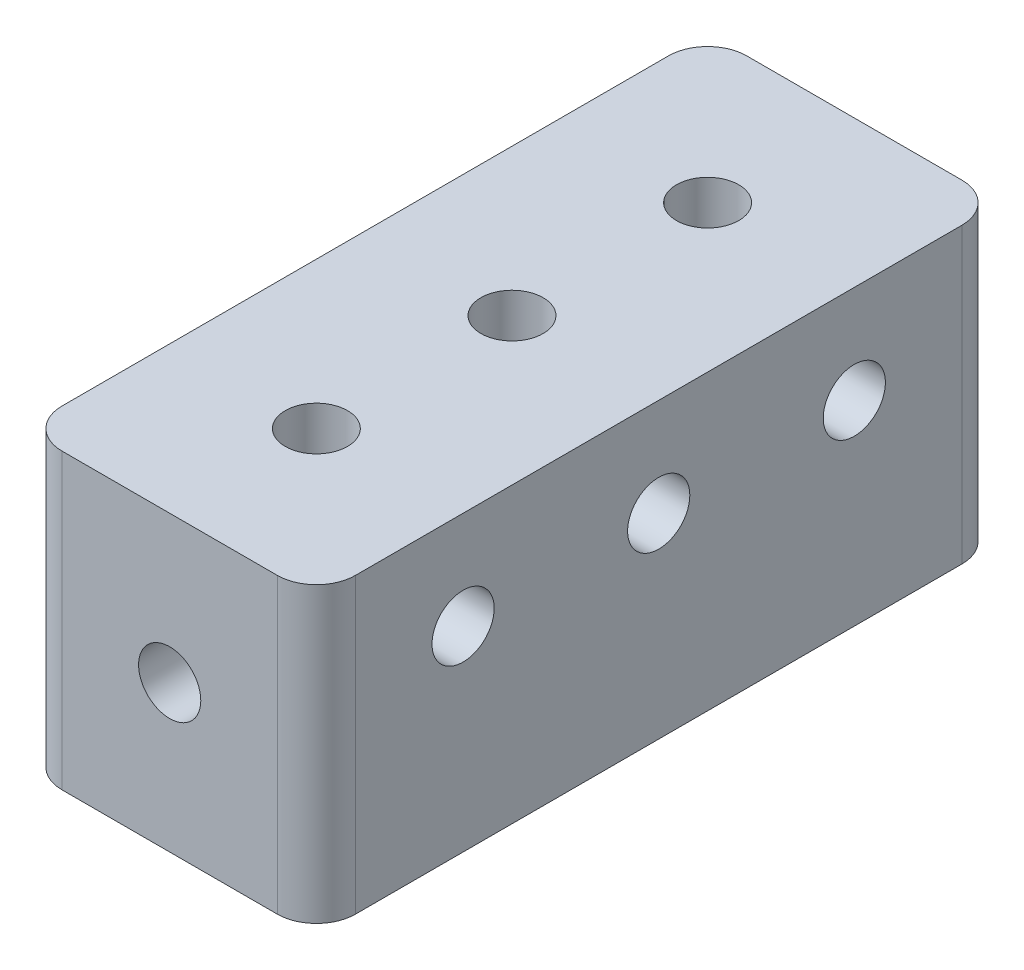
SolidWorks part; units mm, degrees
material "6061-T6 (SS)"
ref_plane "Front Plane" through (0, 0, 0) normal (0, 0, 1) x (1, 0, 0)
ref_plane "Top Plane" through (0, 0, 0) normal (0, 1, 0) x (1, 0, 0)
ref_plane "Right Plane" through (0, 0, 0) normal (1, 0, 0) x (0, 0, -1)
sketch "Sketch1" plane through (0, 0, 0) normal (0, 1, 0) x (1, 0, 0)
  line L1 (-9.525, -22.225) -> (9.525, -22.225)
  line L2 (-9.525, -22.225) -> (-9.525, 22.225)
  line L3 (-9.525, 22.225) -> (9.525, 22.225)
  line L4 (9.525, -22.225) -> (9.525, 22.225)
  line L5 (-9.525, -22.225) -> (9.525, 22.225) construction
  line L6 (-9.525, 22.225) -> (9.525, -22.225) construction
  point P0 (0, 0)
  dimension "D1" = 19.05
  dimension "D2" = 44.45
extrude "Boss-Extrude1" add sketch "Sketch1" along normal mid plane 19.05
sketch "Sketch2" plane through (0, 0, 22.225) normal (0, 0, 1) x (1, 0, 0)
  circle A0 centre (0, 0) radius 2.0193
  dimension "D3" = 4.0386
extrude "Cut-Extrude1" cut sketch "Sketch2" against normal blind 9.525
sketch "Sketch3" plane through (0, 0, -22.225) normal (0, 0, -1) x (-1, 0, 0)
  circle A0 centre (0, 0) radius 2.0193 construction
  circle A1 centre (0, 0) radius 2.0193
extrude "Cut-Extrude2" cut sketch "Sketch3" against normal blind 9.525
sketch "Sketch4" plane through (9.525, 0, 0) normal (1, 0, 0) x (0, 0, -1)
  line L0 (-22.225, 9.525) -> (22.225, 9.525) construction
  circle A0 centre (-12.7, 3.175) radius 2.0193
  circle A1 centre (12.7, 3.175) radius 2.0193
  circle A2 centre (0, 3.175) radius 2.0193
  dimension "D5" = 4.0386
  dimension "D1" = 6.35
  dimension "D3" = 12.7
  dimension "D4" = 12.7
extrude "Cut-Extrude3" cut sketch "Sketch4" against normal blind 6.35
sketch "Sketch5" plane through (-9.525, 0, 0) normal (-1, 0, 0) x (0, 0, 1)
  circle A0 centre (-12.7, 3.175) radius 2.0193 construction
  circle A1 centre (0, 3.175) radius 2.0193 construction
  circle A2 centre (12.7, 3.175) radius 2.0193 construction
  circle A3 centre (-12.7, 3.175) radius 2.0193
  circle A4 centre (0, 3.175) radius 2.0193
  circle A5 centre (12.7, 3.175) radius 2.0193
extrude "Cut-Extrude4" cut sketch "Sketch5" against normal blind 6.35
sketch "Sketch6" plane through (0, 9.525, 0) normal (0, 1, 0) x (1, 0, 0)
  circle A0 centre (0, 12.7) radius 2.0193
  circle A1 centre (0, 0) radius 2.0193
  circle A2 centre (0, -12.7) radius 2.0193
  dimension "D1" = 4.0386
  dimension "D2" = 12.7
  dimension "D3" = 12.7
extrude "Cut-Extrude5" cut sketch "Sketch6" against normal blind 6.35
fillet "Fillet1" radius 2.54 4 edges at (9.525, 0, 22.225) (-9.525, 0, 22.225) (-9.525, 0, -22.225) (9.525, 0, -22.225)
